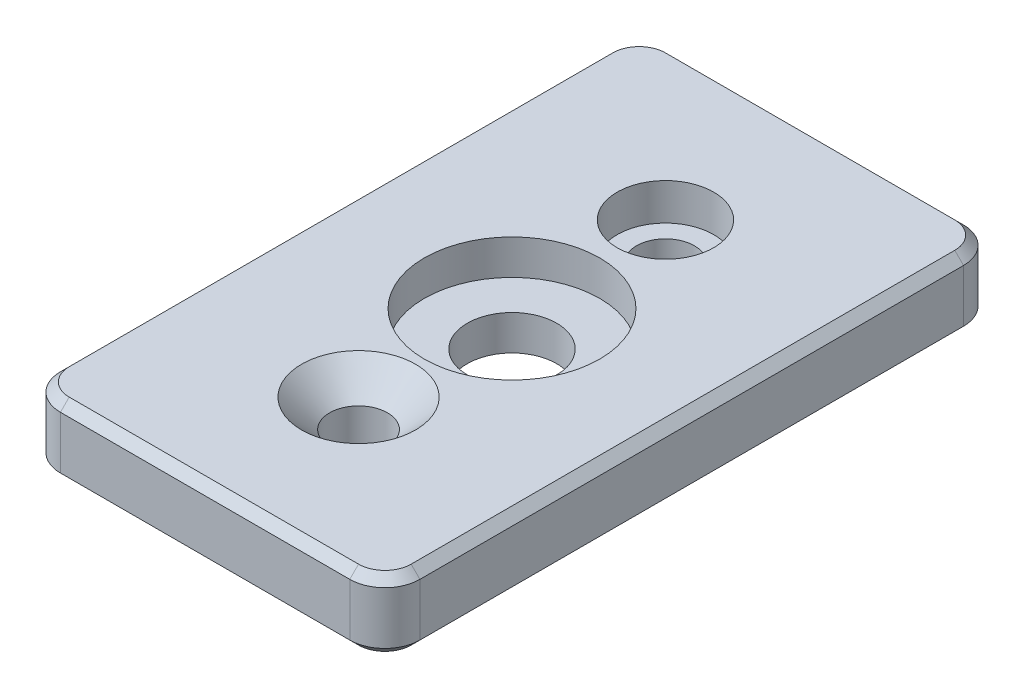
SolidWorks part; units mm, degrees
ref_plane "Front Plane" through (0, 0, 0) normal (0, 0, 1) x (1, 0, 0)
ref_plane "Top Plane" through (0, 0, 0) normal (0, 1, 0) x (1, 0, 0)
ref_plane "Right Plane" through (0, 0, 0) normal (1, 0, 0) x (0, 0, -1)
sketch "Sketch1" plane through (0, 0, 0) normal (0, 1, 0) x (1, 0, 0)
  line L1 (-20.5, 35) -> (20.5, 35)
  line L2 (-20.5, 35) -> (-20.5, -35)
  line L3 (-20.5, -35) -> (20.5, -35)
  line L4 (20.5, 35) -> (20.5, -35)
  line L5 (-20.5, 35) -> (20.5, -35) construction
  line L6 (-20.5, -35) -> (20.5, 35) construction
  point P0 (0, 0)
  dimension "D1" = 70
  dimension "D2" = 41
extrude "Boss-Extrude1" add sketch "Sketch1" along normal blind 8
fillet "Fillet1" radius 4 4 edges at (-20.5, 4, -35) (20.5, 4, -35) (20.5, 4, 35) (-20.5, 4, 35)
chamfer "Chamfer1" distance 1 angle 45 16 edges at (0, 0, 35) (19.3284, 0, 33.8284) (20.5, 0, 0) (19.3284, 0, -33.8284) (0, 0, -35) (-19.3284, 0, -33.8284) (-20.5, 0, 0) (-19.3284, 0, 33.8284) (19.3284, 8, 33.8284) (20.5, 8, 0) (19.3284, 8, -33.8284) (0, 8, -35) (-19.3284, 8, -33.8284) (-20.5, 8, 0) (-19.3284, 8, 33.8284) (0, 8, 35)
sketch "Sketch2" plane through (0, 8, 0) normal (0, 1, 0) x (1, 0, 0)
  line L0 (16.5, -35) -> (-16.5, -35) construction
  line L1 (-16.5, 35) -> (16.5, 35) construction
  circle A0 centre (0, -17.5) radius 3.3
  circle A1 centre (0, 17.5) radius 3.3
  dimension "D1" = 17.5
  dimension "D2" = 17.5
extrude "Cut-Extrude1" cut sketch "Sketch2" against normal blind 8
chamfer "Chamfer2" distance 3.2 angle 45 1 edges at (0, 8, 20.8)
sketch "Sketch3" plane through (0, 8, 0) normal (0, 1, 0) x (1, 0, 0)
  circle A0 centre (0, 17.5) radius 5.5
extrude "Cut-Extrude2" cut sketch "Sketch3" against normal blind 4.2
sketch "Sketch4" plane through (0, 8, 0) normal (0, 1, 0) x (1, 0, 0)
  circle A0 centre (0, 0) radius 5.1
extrude "Cut-Extrude3" cut sketch "Sketch4" against normal blind 10
sketch "Sketch5" plane through (0, 8, 0) normal (0, 1, 0) x (1, 0, 0)
  circle A0 centre (0, 0) radius 10
extrude "Cut-Extrude5" cut sketch "Sketch5" against normal blind 4
